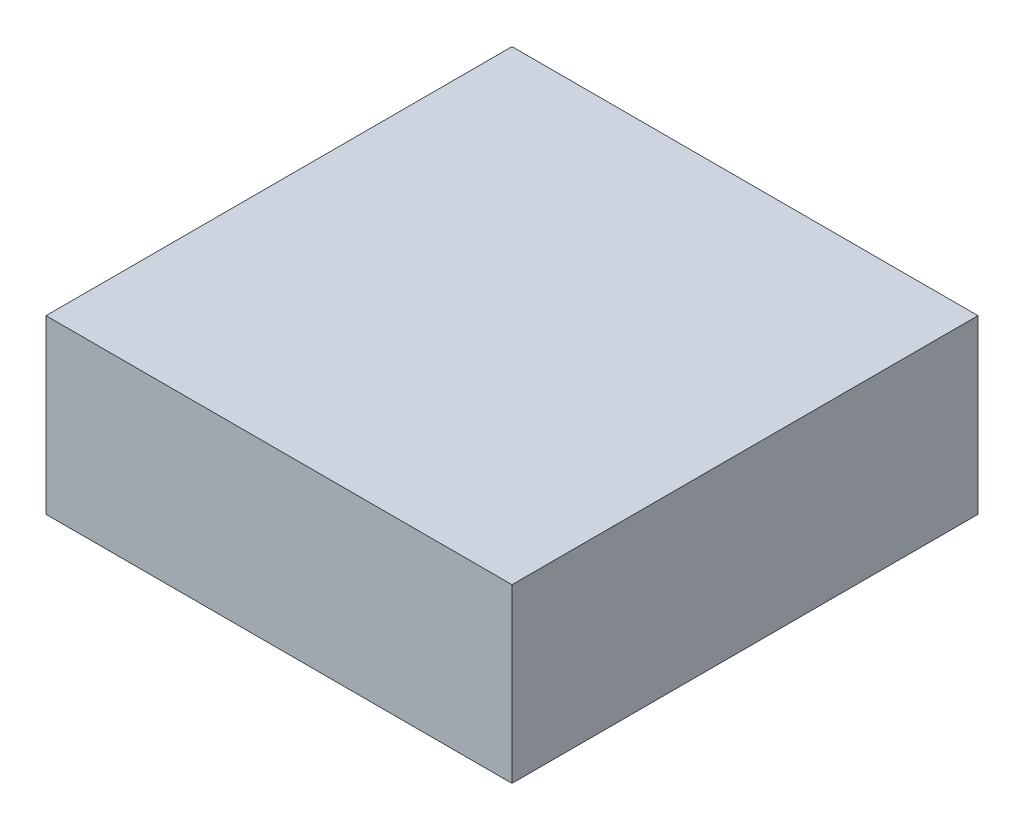
SolidWorks part; units mm, degrees
material "Silicon Dioxide"
ref_plane "Front Plane" through (0, 0, 0) normal (0, 0, 1) x (1, 0, 0)
ref_plane "Top Plane" through (0, 0, 0) normal (0, 1, 0) x (1, 0, 0)
ref_plane "Right Plane" through (0, 0, 0) normal (1, 0, 0) x (0, 0, -1)
sketch "Sketch1" plane through (0, 0, 0) normal (0, 1, 0) x (1, 0, 0)
  line L1 (-0.8125, -0.8125) -> (0.8125, -0.8125)
  line L2 (-0.8125, -0.8125) -> (-0.8125, 0.8125)
  line L3 (-0.8125, 0.8125) -> (0.8125, 0.8125)
  line L4 (0.8125, -0.8125) -> (0.8125, 0.8125)
  line L5 (-0.8125, -0.8125) -> (0.8125, 0.8125) construction
  line L6 (-0.8125, 0.8125) -> (0.8125, -0.8125) construction
  point P0 (0, 0)
  dimension "D1" = 1.625
  dimension "D2" = 1.625
extrude "Boss-Extrude1" add sketch "Sketch1" along normal blind 0.6
